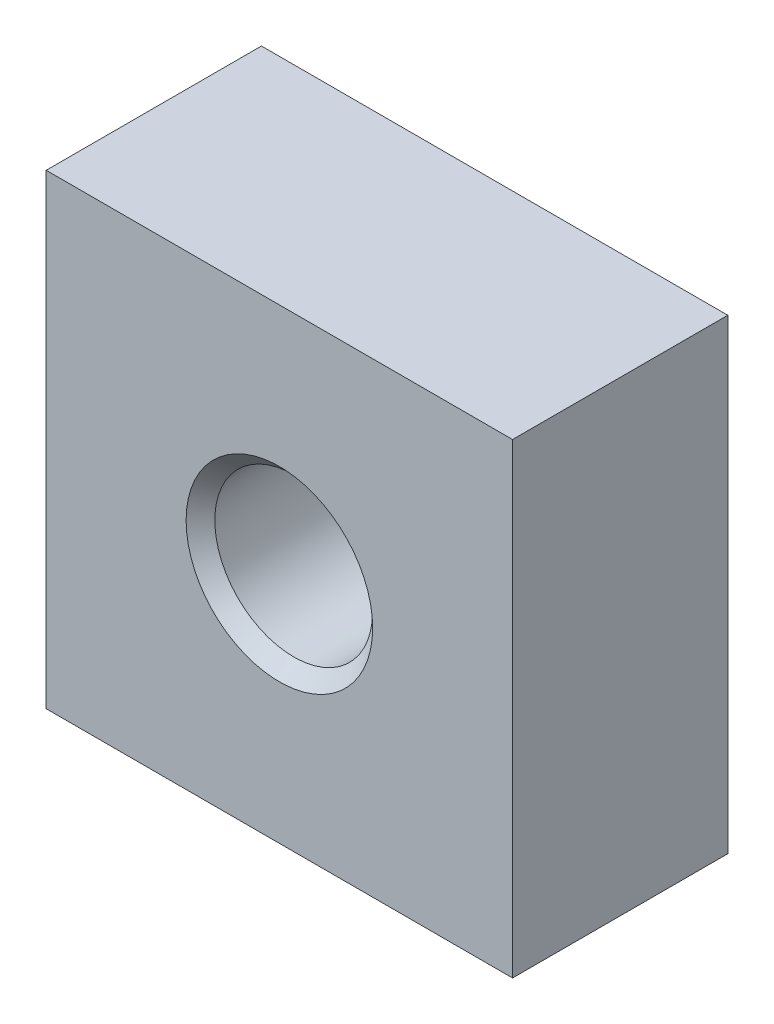
SolidWorks part; units mm, degrees
material "AISI 304"
ref_plane "Спереди" through (0, 0, 0) normal (0, 0, 1) x (1, 0, 0)
ref_plane "Сверху" through (0, 0, 0) normal (0, 1, 0) x (1, 0, 0)
ref_plane "Справа" through (0, 0, 0) normal (1, 0, 0) x (0, 0, -1)
sketch "Эскиз1" plane through (0, 0, 0) normal (0, 0, 1) x (1, 0, 0)
  line L1 (32.5, -32.5) -> (-32.5, -32.5)
  line L2 (32.5, -32.5) -> (32.5, 32.5)
  line L3 (32.5, 32.5) -> (-32.5, 32.5)
  line L4 (-32.5, -32.5) -> (-32.5, 32.5)
  line L5 (32.5, -32.5) -> (-32.5, 32.5) construction
  line L6 (32.5, 32.5) -> (-32.5, -32.5) construction
  circle A0 centre (0, 0) radius 11
  point P0 (0, 0)
  dimension "D2" = 22
  dimension "D1" = 65
extrude "Бобышка-Вытянуть1" add sketch "Эскиз1" along normal blind 30
chamfer "Фаска1" distance 2 angle 45 2 edges at (11, 0, 0) (11, 0, 30)
